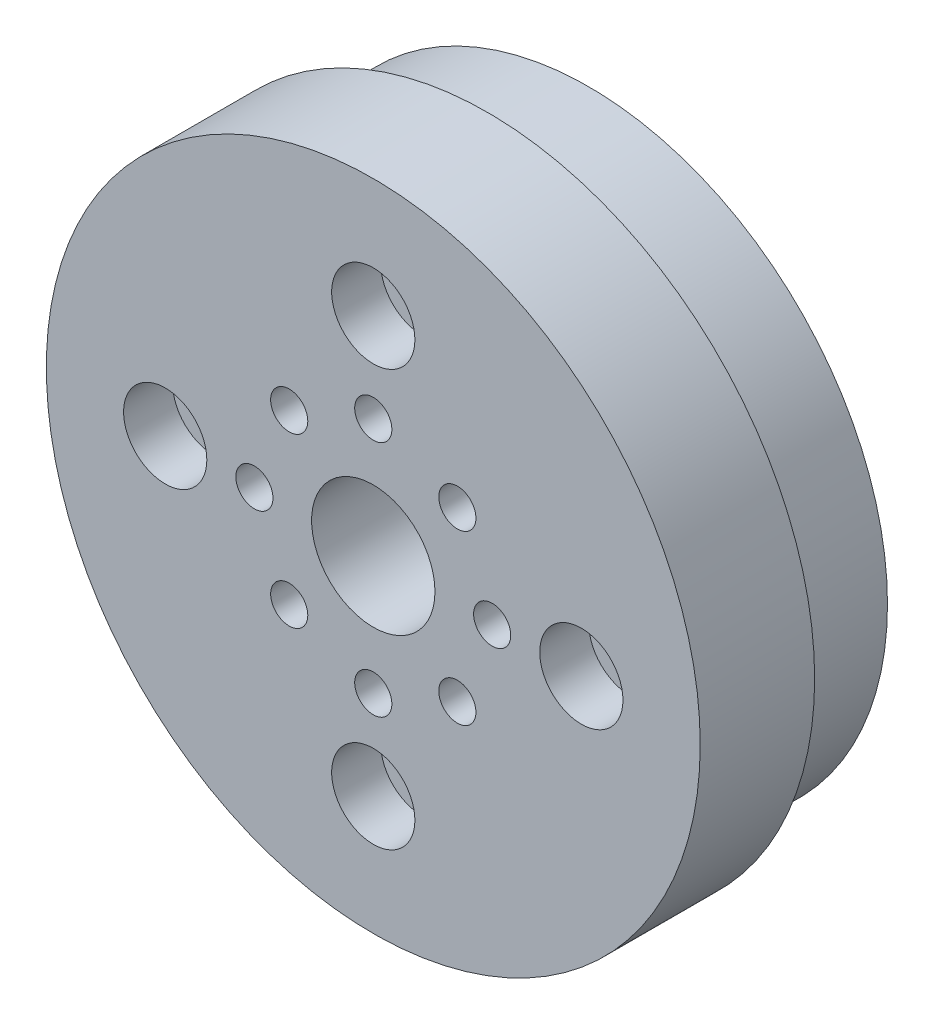
SolidWorks part; units mm, degrees
ref_plane "Front Plane" through (0, 0, 0) normal (0, 0, 1) x (1, 0, 0)
ref_plane "Top Plane" through (0, 0, 0) normal (0, 1, 0) x (1, 0, 0)
ref_plane "Right Plane" through (0, 0, 0) normal (1, 0, 0) x (0, 0, -1)
sketch "Sketch1" plane through (0, 0, 0) normal (0, 0, 1) x (1, 0, 0)
  circle A0 centre (0, 0) radius 22
extrude "Boss-Extrude1" add sketch "Sketch1" along normal blind 7.7 contours A0
sketch "Sketch2" plane through (0, 0, 0) normal (0, 0, -1) x (-1, 0, 0)
  circle A0 centre (0, 0) radius 20.1
  circle A1 centre (0, 0) radius 18.1
  dimension "D1" = 40.2
  dimension "D2" = 2
extrude "Boss-Extrude2" add sketch "Sketch2" along normal blind 6.8
sketch "Sketch3" plane through (0, 0, 7.7) normal (0, 0, 1) x (1, 0, 0)
  circle A0 centre (0, 0) radius 4.15
  circle A1 centre (0, 8) radius 1.25
  circle A2 centre (5.6569, 5.6569) radius 1.25
  circle A3 centre (8, 0) radius 1.25
  circle A4 centre (5.6569, -5.6569) radius 1.25
  circle A5 centre (0, -8) radius 1.25
  circle A6 centre (-5.6569, -5.6569) radius 1.25
  circle A7 centre (-8, 0) radius 1.25
  circle A8 centre (-5.6569, 5.6569) radius 1.25
  point P22 (0, 0)
  dimension "D1" = 8.3
  dimension "D2" = 8
  dimension "D3" = 8
extrude "Cut-Extrude1" cut sketch "Sketch3" against normal through all
sketch "Sketch4" plane through (0, 0, 7.7) normal (0, 0, 1) x (1, 0, 0)
  circle A0 centre (14, 0) radius 2.8
  circle A1 centre (0, -14) radius 2.8
  circle A2 centre (-14, 0) radius 2.8
  circle A3 centre (0, 14) radius 2.8
  point P12 (0, 0)
  dimension "D1" = 5.6
  dimension "D2" = 14
  dimension "D3" = 4
extrude "Cut-Extrude2" cut sketch "Sketch4" against normal blind 3.3
sketch "Sketch6" plane through (0, 0, 7.7) normal (0, 0, 1) x (1, 0, 0)
  circle A0 centre (14, 0) radius 1.6
  circle A1 centre (0, -14) radius 1.6
  circle A2 centre (-14, 0) radius 1.6
  circle A3 centre (0, 14) radius 1.6
  point P12 (0, 0)
  dimension "D1" = 3.2
  dimension "D2" = 4
extrude "Cut-Extrude3" cut sketch "Sketch6" against normal through all
